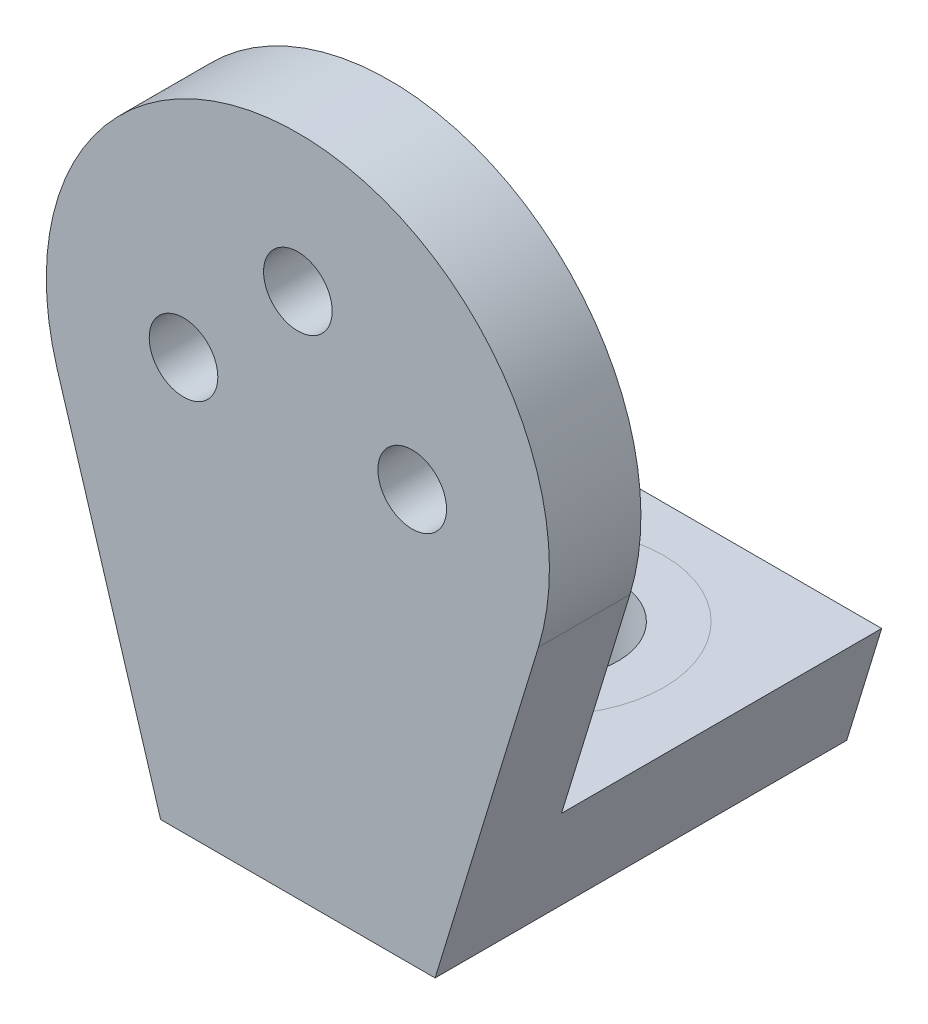
SolidWorks part; units mm, degrees
material "1060 Alloy"
ref_plane "Front Plane" through (0, 0, 0) normal (0, 0, 1) x (1, 0, 0)
ref_plane "Top Plane" through (0, 0, 0) normal (0, 1, 0) x (1, 0, 0)
ref_plane "Right Plane" through (0, 0, 0) normal (1, 0, 0) x (0, 0, -1)
sketch "Sketch1" plane through (0, 0, 0) normal (0, 0, 1) x (1, 0, 0)
  circle A1 centre (0, 0) radius 55
  dimension "D2" = 110
extrude "Boss-Extrude1" add sketch "Sketch1" along normal blind 20
sketch "Sketch2" plane through (0, 0, 20) normal (0, 0, 1) x (1, 0, 0)
  line L0 (-52.5973, -16.0787) -> (-30, -90)
  line L1 (0, 0) -> (0, -114.253) construction
  line L2 (-30, -90) -> (30, -90)
  line L3 (52.5973, -16.0787) -> (30, -90)
  circle A0 centre (0, 0) radius 55 construction
  circle A1 centre (0, 0) radius 55
  point P9 (0, -90)
  circle M4 centre (0, 0) radius 55
  dimension "D1" = 60
  dimension "D2" = 90
extrude "Boss-Extrude2" add sketch "Sketch2" against normal up to surface (20 mm away) contours A1 L1 L2 L3 | L1 L0 L2 M4
sketch "Sketch3" plane through (0, 0, 0) normal (0, 0, -1) x (-1, 0, 0)
  text T0 "TforDesign" font "Century Gothic" height in points 24
extrude "Cut-Extrude1" [suppressed] cut sketch "Sketch3" against normal blind 1
sketch "Sketch4" plane through (0, 0, 0) normal (0, 0, -1) x (-1, 0, 0)
  line L0 (0, 0) -> (0, -12.8185) construction
  circle A0 centre (0, 25) radius 7.5
  circle A1 centre (-25, 0) radius 7.5
  circle A2 centre (25, 0) radius 7.5
  dimension "D1" = 15
  dimension "D2" = 25
  dimension "D3" = 25
extrude "Cut-Extrude2" cut sketch "Sketch4" against normal up to next
sketch "Sketch5" plane through (0, 0, 0) normal (0, 0, -1) x (-1, 0, 0)
  line L0 (-37.6423, -65) -> (37.6423, -65)
  line L3 (-52.5973, -16.0787) -> (-30, -90)
  line L4 (-30, -90) -> (30, -90)
  line L5 (30, -90) -> (52.5973, -16.0787)
  line L6 (-52.5973, -16.0787) -> (-30, -90)
  line L7 (-30, -90) -> (30, -90)
  line L8 (30, -90) -> (52.5973, -16.0787)
  arc A1 (52.5973, -16.0787) -> (-52.5973, -16.0787) centre (0, 0) ccw
  arc A2 (52.5973, -16.0787) -> (-52.5973, -16.0787) centre (0, 0) ccw
  dimension "D2" = 25
  dimension "D1" = 0
extrude "Boss-Extrude3" add sketch "Sketch5" along normal blind 70 contours L7 L8 L0 L6
sketch "Sketch6" plane through (0, -65, 0) normal (0, 1, 0) x (1, 0, 0)
  line L0 (37.6423, 70) -> (-37.6423, 0) construction
  circle A0 centre (0, 35) radius 15
  dimension "D1" = 30
extrude "Cut-Extrude3" cut sketch "Sketch6" against normal up to next
fillet "Fillet3" [suppressed] radius 2
sketch "Sketch8" plane through (0, -65, 0) normal (0, 1, 0) x (1, 0, 0)
  circle A0 centre (0, 35) radius 25
  dimension "D1" = 50
split line "Split Line1"
ref_plane "Plane1" through (0, 0, 20) normal (0, 0, 1) x (1, 0, 0)
